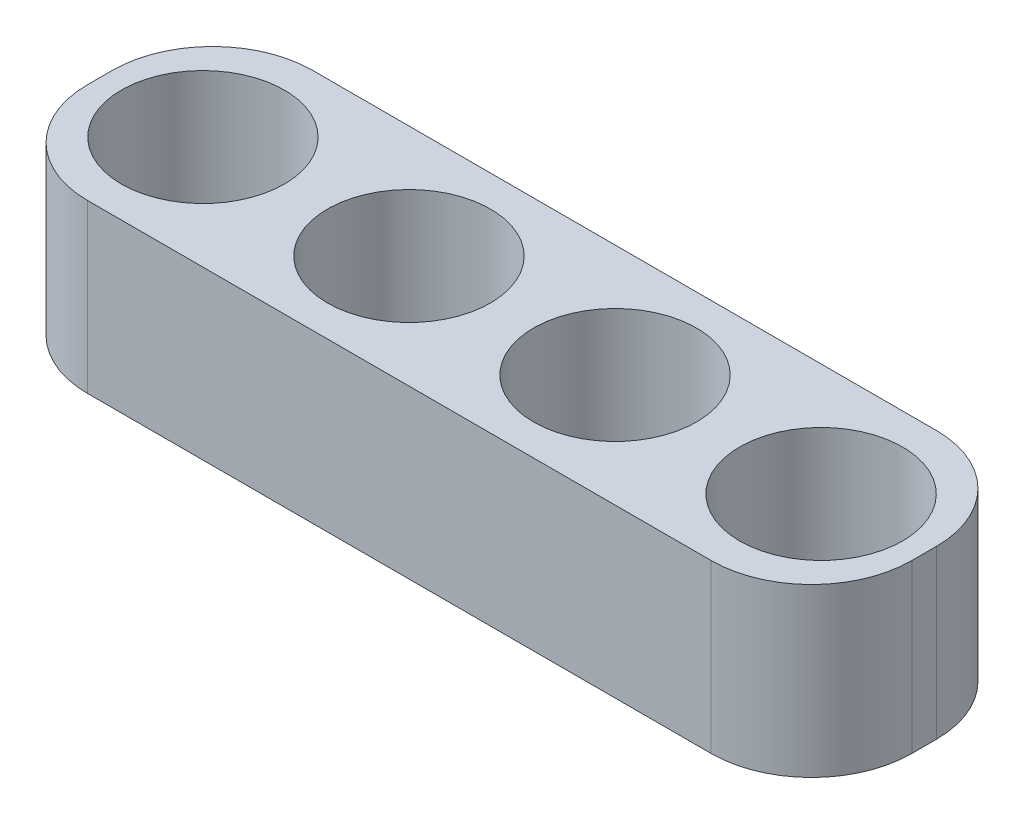
SolidWorks part; units mm, degrees
ref_plane "Front Plane" through (0, 0, 0) normal (0, 0, 1) x (1, 0, 0)
ref_plane "Top Plane" through (0, 0, 0) normal (0, 1, 0) x (1, 0, 0)
ref_plane "Right Plane" through (0, 0, 0) normal (1, 0, 0) x (0, 0, -1)
sketch "Sketch1" plane through (0, 0, 0) normal (0, 1, 0) x (1, 0, 0)
  line L0 (0, 13.4766) -> (0, -13.4766)
  line L1 (-49.3187, -13.4766) -> (49.3187, -13.4766)
  line L2 (-49.3187, -13.4766) -> (-49.3187, 13.4766)
  line L3 (-49.3187, 13.4766) -> (49.3187, 13.4766)
  line L4 (49.3187, -13.4766) -> (49.3187, 13.4766)
  line L5 (-49.3187, -13.4766) -> (49.3187, 13.4766) construction
  line L6 (-49.3187, 13.4766) -> (49.3187, -13.4766) construction
  line L7 (-49.3187, 13.4766) -> (0, 13.4766)
  line L8 (0, 13.4766) -> (49.3187, 13.4766)
  line L9 (-24.6593, 13.4766) -> (-24.6593, -13.4766)
  line L10 (0, 13.4766) -> (49.3187, 13.4766)
  line L11 (24.6593, 13.4766) -> (24.6593, -13.4766)
  line L12 (-49.3187, 13.4766) -> (-24.6593, -13.4766)
  line L13 (-24.6593, 13.4766) -> (0, -13.4766)
  line L14 (0, 13.4766) -> (24.6593, -13.4766)
  line L15 (24.6593, 13.4766) -> (49.3187, -13.4766)
  circle A0 centre (-36.989, 0) radius 9.75
  circle A1 centre (-12.3297, 0) radius 9.75
  circle A2 centre (12.3297, 0) radius 9.75
  circle A3 centre (36.989, 0) radius 9.75
  point P0 (0, 0)
extrude "Boss-Extrude1" add sketch "Sketch1" along normal blind 20 contours A0 L12 L9 L3 | A0 L12 L2 L1 | A1 L13 L0 L7 | A1 L13 L9 L1 | A2 L14 L11 L3 | A2 L14 L0 L1 | A3 L15 L4 L10 | A3 L15 L11 L1
fillet "Fillet2" radius 12 4 edges at (49.3187, 10, 13.4766) (49.3187, 10, -13.4766) (-49.3187, 10, 13.4766) (-49.3187, 10, -13.4766)
